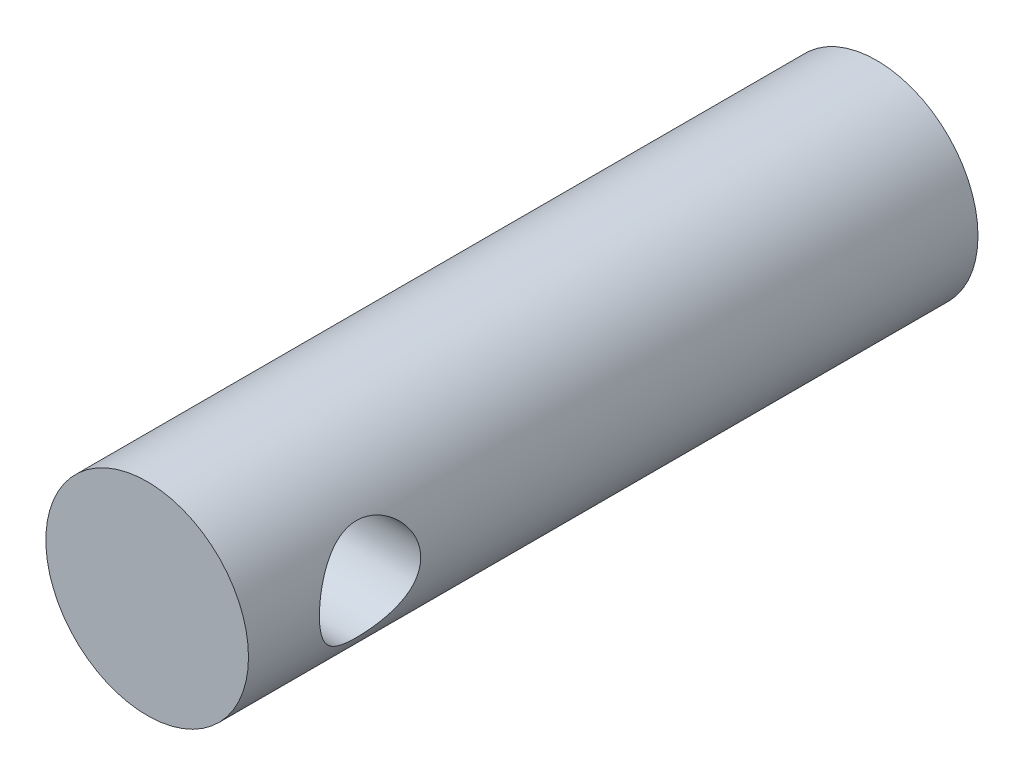
SolidWorks part; units mm, degrees
material "AISI 304"
ref_plane "Front Plane" through (0, 0, 0) normal (0, 0, 1) x (1, 0, 0)
ref_plane "Top Plane" through (0, 0, 0) normal (0, 1, 0) x (1, 0, 0)
ref_plane "Right Plane" through (0, 0, 0) normal (1, 0, 0) x (0, 0, -1)
sketch "Sketch1" plane through (0, 0, 0) normal (0, 0, 1) x (1, 0, 0)
  circle A0 centre (0, 0) radius 2.5
extrude "Boss-Extrude1" add sketch "Sketch1" along normal blind 18
sketch "Sketch2" plane through (0, 0, 0) normal (1, 0, 0) x (0, 0, -1)
  line L0 (-18, -2.5) -> (0, -2.5) construction
  line L1 (-18, 2.5) -> (-18, -2.5) construction
  circle A0 centre (-15, 0) radius 1.25
  dimension "D1" = 2.5
  dimension "D2" = 3
extrude "Cut-Extrude2" cut sketch "Sketch2" against normal through all both and the other way through all
